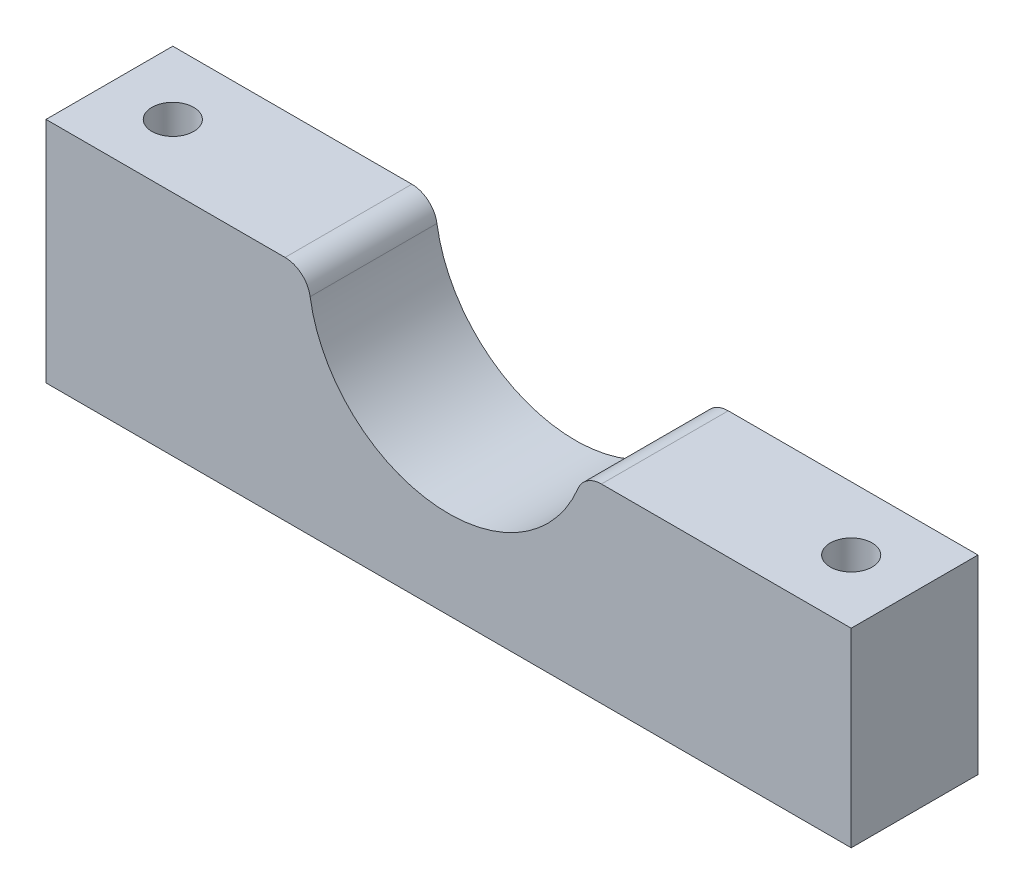
SolidWorks part; units mm, degrees
ref_plane "Спереди" through (0, 0, 0) normal (0, 0, 1) x (1, 0, 0)
ref_plane "Сверху" through (0, 0, 0) normal (0, 1, 0) x (1, 0, 0)
ref_plane "Справа" through (0, 0, 0) normal (1, 0, 0) x (0, 0, -1)
sketch "Эскиз1" plane through (0, 0, 0) normal (0, 0, 1) x (1, 0, 0)
  line L0 (0, 24.9844) -> (0, -42.4233) construction
  line L2 (-31.75, 0) -> (-11.05, 0)
  line L3 (-31.75, 0) -> (-31.75, -18)
  line L4 (-31.75, -18) -> (31.75, -18)
  line L5 (31.75, -3) -> (31.75, -18)
  line L6 (-31.75, 0) -> (31.75, -18) construction
  line L7 (-31.75, -18) -> (32.1667, 0.1181) construction
  line L8 (10.635, -3) -> (31.75, -3)
  arc A0 (-11.05, 0) -> (10.635, -3) centre (0, 0) ccw
  point P5 (0, -9)
  dimension "D1" = 22.1
  dimension "D2" = 63.5
  dimension "D3" = 18
  dimension "D4" = 31.75
  dimension "D5" = 15
extrude "Бобышка-Вытянуть1" add sketch "Эскиз1" along normal blind 10
sketch "Эскиз2" plane through (0, -18, 0) normal (0, -1, 0) x (1, 0, 0)
  line L0 (-31.75, 5) -> (31.75, 5) construction
  line L1 (-31.75, 10) -> (-31.75, 0) construction
  line L2 (31.75, 10) -> (31.75, 0) construction
  line L3 (-26.75, 10) -> (-26.75, 0) construction
  line L4 (-31.75, 10) -> (31.75, 10) construction
  line L5 (-31.75, 0) -> (31.75, 0) construction
  line L6 (26.75, 10) -> (26.75, 0) construction
  dimension "D1" = 5
  dimension "D2" = 5
hole_wizard "Отверстие обработанное метчиком M4x0.71" positions "Эскиз4" profile "Эскиз3" tap size "M4x0.7" standard "Ansi Metric" end condition through all
sketch "Эскиз4" plane through (0, -18, 0) normal (0, -1, 0) x (-1, 0, 0)
  line L0 (26.75, -10) -> (26.75, 0) construction
  line L1 (-26.75, -10) -> (-26.75, 0) construction
  point P0 (26.75, -5)
  point P4 (-26.75, -5)
sketch "Эскиз3" plane through (-26.75, -18, 5) normal (1, 0, 0) x (0, 0, -1)
  line L0 (0, 0) -> (0, 18)
  line L1 (0, 18) -> (1.65, 18)
  line L2 (1.65, 18) -> (1.65, 0)
  line L5 (1.65, 0) -> (0, 0)
  line L11 (0, -6.35) -> (0, 107.95) construction
  dimension "Диаметр проходного сверла" = 3.3
  dimension "Глубина проходного сверла" = 18
cosmetic thread "Отверстие резьбы1" parameters "D2"=4
cosmetic thread "Отверстие резьбы2" parameters "D2"=4
fillet "Скругление2" radius 2 2 edges at (-11.05, 0, 5) (10.635, -3, 5)
fillet "Скругление1" [suppressed] radius 0.5
